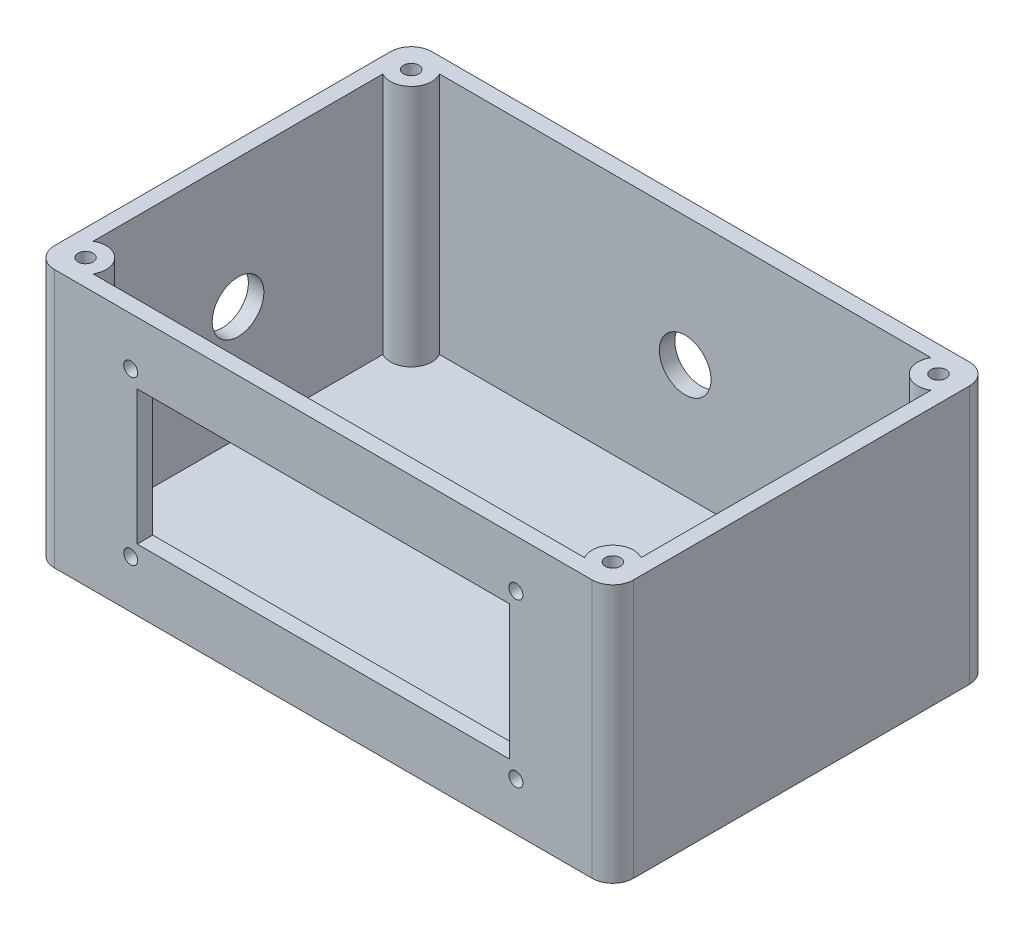
SolidWorks part; units mm, degrees
ref_plane "Front Plane" through (0, 0, 0) normal (0, 0, 1) x (1, 0, 0)
ref_plane "Top Plane" through (0, 0, 0) normal (0, 1, 0) x (1, 0, 0)
ref_plane "Right Plane" through (0, 0, 0) normal (1, 0, 0) x (0, 0, -1)
sketch "Sketch2" plane through (0, 0, 0) normal (0, 1, 0) x (1, 0, 0)
  line L1 (-56, 36.5) -> (56, 36.5)
  line L2 (-56, 36.5) -> (-56, -36.5)
  line L3 (-56, -36.5) -> (56, -36.5)
  line L4 (56, 36.5) -> (56, -36.5)
  line L5 (-56, 36.5) -> (56, -36.5) construction
  line L6 (-56, -36.5) -> (56, 36.5) construction
  point P0 (0, 0)
  point P11 (0, 0)
  point P16 (0, 0)
  dimension "D1" = 73
  dimension "D2" = 112
extrude "Boss-Extrude1" add sketch "Sketch2" along normal blind 50
shell "Shell3" thickness 3
sketch "Sketch3" plane through (0, 0, 36.5) normal (0, 0, 1) x (1, 0, 0)
  line L0 (-56, 50) -> (56, 50) construction
  line L1 (-36, 38) -> (36, 38)
  line L2 (-36, 38) -> (-36, 12)
  line L3 (-36, 12) -> (36, 12)
  line L4 (36, 38) -> (36, 12)
  line L5 (-36, 38) -> (36, 12) construction
  line L6 (-36, 12) -> (36, 38) construction
  point P0 (0, 25)
  point P8 (0, 25)
  dimension "D1" = 72
  dimension "D2" = 26
  dimension "D3" = 12
ref_plane "Plane5" through (0, 2.5, 0) normal (0, 1, 0) x (1, 0, 0)
sketch "Sketch5" plane through (0, 2.5, 0) normal (0, 1, 0) x (1, 0, 0)
  line L1 (56, 36.5) -> (-56, 36.5) construction
  line L2 (-56, 36.5) -> (-56, -36.5) construction
  circle A1 centre (-51, 31.5) radius 4
  circle A2 centre (-51, -31.5) radius 4
  circle A3 centre (51, 31.5) radius 4
  circle A4 centre (51, -31.5) radius 4
  point P14 (0, 0)
  point P18 (0, 0)
  dimension "D1" = 5
  dimension "D3" = 8
  dimension "D2" = 5
extrude "Boss-Extrude2" add sketch "Sketch5" along normal blind 47.5
extrude "Cut-Extrude1" cut sketch "Sketch3" against normal up to next
sketch "Sketch6" plane through (0, 50, 0) normal (0, 1, 0) x (1, 0, 0)
  line L0 (56, -36.5) -> (56, 36.5) construction
  line L1 (56, 36.5) -> (-56, 36.5) construction
  line L6 (-19.8567, 48.1184) -> (-20.1429, 48.9051) construction
  circle A0 centre (51, 31.5) radius 1.47
  circle A1 centre (51, -31.5) radius 1.47
  circle A2 centre (-51, -31.5) radius 1.47
  circle A3 centre (-51, 31.5) radius 1.47
  dimension "D1" = 5
  dimension "D2" = 5
extrude "Cut-Extrude2" cut sketch "Sketch6" against normal blind 10
fillet "Fillet1" radius 4 4 edges at (-56, 25, -36.5) (-56, 25, 36.5) (56, 25, 36.5) (56, 25, -36.5)
sketch "Sketch7" plane through (0, 0, 36.5) normal (0, 0, 1) x (1, 0, 0)
  line L0 (-36, 38) -> (-36, 12) construction
  line L1 (36, 38) -> (-36, 38) construction
  circle A0 centre (-37.26, 40.74) radius 1.35
  circle A1 centre (-37.26, 9.26) radius 1.35
  circle A2 centre (37.26, 40.74) radius 1.35
  circle A3 centre (37.26, 9.26) radius 1.35
  dimension "D1" = 2.7
  dimension "D2" = 1.26
  dimension "D3" = 2.74
extrude "Cut-Extrude3" cut sketch "Sketch7" against normal up to next
sketch "Sketch8" plane through (0, 0, -36.5) normal (0, 0, -1) x (-1, 0, 0)
  line L0 (-52, 0) -> (52, 0) construction
  line L1 (52, 0) -> (52, 50) construction
  circle A0 centre (0, 25) radius 5
  point P2 (0, 0)
  point P5 (0, 0)
  point P6 (0, 0)
  point P9 (52, 25)
  dimension "D1" = 10
extrude "Cut-Extrude4" cut sketch "Sketch8" against normal up to next
sketch "Sketch9" plane through (-56, 0, 0) normal (-1, 0, 0) x (0, 0, 1)
  line L0 (-32.5, 0) -> (32.5, 0) construction
  line L1 (32.5, 0) -> (32.5, 50) construction
  circle A0 centre (0, 25) radius 5
  point P4 (0, 0)
  point P5 (0, 0)
  point P6 (0, 0)
  point P7 (0, 0)
  point P10 (32.5, 25)
  dimension "D1" = 10
extrude "Cut-Extrude5" cut sketch "Sketch9" against normal up to next
